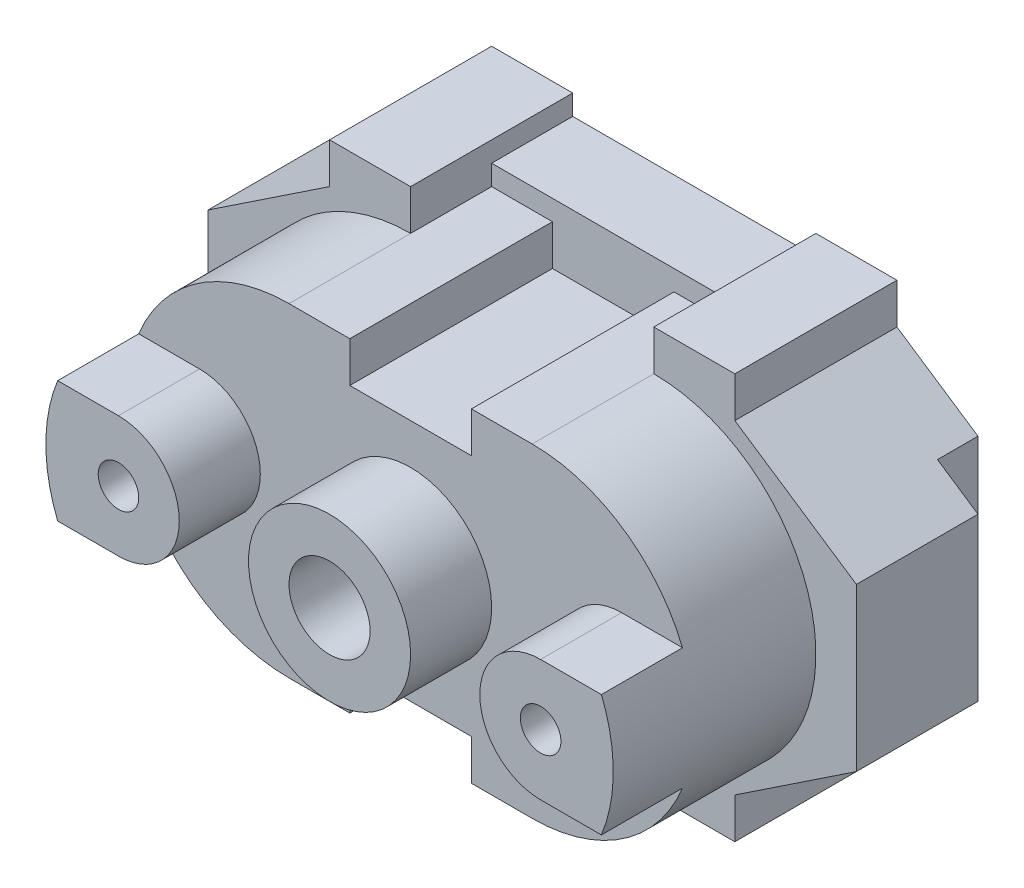
SolidWorks part; units mm, degrees
ref_plane "Front Plane" through (0, 0, 0) normal (0, 0, 1) x (1, 0, 0)
ref_plane "Top Plane" through (0, 0, 0) normal (0, 1, 0) x (1, 0, 0)
ref_plane "Right Plane" through (0, 0, 0) normal (1, 0, 0) x (0, 0, -1)
sketch "Sketch1" plane through (0, 0, 0) normal (0, 0, 1) x (1, 0, 0)
  line L0 (-80, 0) -> (-65, 10)
  line L1 (-65, 10) -> (-65, 15)
  line L2 (-65, 15) -> (-55, 15)
  line L3 (-55, 15) -> (-55, 10)
  line L4 (-55, 10) -> (-25, 10)
  line L5 (-25, 10) -> (-25, 15)
  line L6 (-25, 15) -> (-15, 15)
  line L7 (-15, 15) -> (-15, 10)
  line L8 (-15, 10) -> (0, 0)
  line L9 (0, 0) -> (0, -20)
  line L10 (0, -20) -> (-15, -30)
  line L11 (-15, -30) -> (-15, -35)
  line L12 (-15, -35) -> (-25, -35)
  line L13 (-25, -35) -> (-25, -30)
  line L14 (-25, -30) -> (-55, -30)
  line L15 (-55, -30) -> (-55, -35)
  line L16 (-55, -35) -> (-65, -35)
  line L17 (-65, -35) -> (-65, -30)
  line L18 (-65, -30) -> (-80, -20)
  line L19 (-80, -20) -> (-80, 0)
  dimension "D1" = 10
  dimension "D2" = 10
  dimension "D3" = 5
  dimension "D4" = 5
  dimension "D5" = 5
  dimension "D6" = 5
  dimension "D7" = 20
  dimension "D8" = 20
  dimension "D9" = 5
  dimension "D10" = 10
  dimension "D11" = 5
  dimension "D12" = 30
  dimension "D13" = 15
  dimension "D14" = 10
  dimension "D15" = 5
  dimension "D16" = 5
  dimension "D17" = 10
  dimension "D18" = 15
  dimension "D19" = 10
  dimension "D20" = 15
  dimension "D21" = 10
  dimension "D22" = 15
extrude "Boss-Extrude1" add sketch "Sketch1" along normal blind 20
sketch "Sketch2" plane through (-80, 0, 0) normal (-1, 0, 0) x (0, 0, 1)
  line L1 (0, -23.75) -> (0, 3.75)
  line L2 (0, 3.75) -> (5, 3.75)
  line L3 (5, 3.75) -> (5, -23.75)
  line L4 (5, -23.75) -> (0, -23.75)
  line L5 (20, -20) -> (0, -20) construction
  dimension "D1" = 27.5
  dimension "D2" = 5
  dimension "D3" = 3.75
extrude "Cut-Extrude2" cut sketch "Sketch2" against normal blind 5
sketch "Sketch3" plane through (0, 0, 0) normal (1, 0, 0) x (0, 0, -1)
  line L0 (0, 3.75) -> (0, -23.75)
  line L1 (0, -23.75) -> (-5, -23.75)
  line L2 (-5, -23.75) -> (-5, 3.75)
  line L3 (-5, 3.75) -> (0, 3.75)
  line L4 (-20, 0) -> (0, 0) construction
  dimension "D1" = 5
  dimension "D2" = 27.5
  dimension "D3" = 3.75
extrude "Cut-Extrude3" cut sketch "Sketch3" against normal blind 5
sketch "Sketch4" plane through (0, 0, 20) normal (0, 0, 1) x (1, 0, 0)
  line L0 (-55, -10) -> (-25, -10) construction
  line L1 (-55, 10) -> (-25, 10)
  line L2 (-55, -30) -> (-25, -30)
  arc A0 (-55, 10) -> (-55, -30) centre (-55, -10) ccw
  arc A1 (-25, -30) -> (-25, 10) centre (-25, -10) ccw
  point P2 (-40, -10)
  dimension "D1" = 20
extrude "Boss-Extrude2" add sketch "Sketch4" along normal blind 15
sketch "Sketch5" plane through (0, 0, 0) normal (0, 0, -1) x (-1, 0, 0)
  line L0 (25, -32.5) -> (25, -30)
  line L1 (25, -30) -> (25, -35) construction
  line L2 (25, -30) -> (55, -30)
  line L3 (55, -30) -> (55, -32.5)
  line L4 (55, -35) -> (55, -30) construction
  line L5 (55, -32.5) -> (25, -32.5)
  line L7 (25, 12.5) -> (25, 10)
  line L8 (25, 15) -> (25, 10) construction
  line L9 (25, 10) -> (55, 10)
  line L10 (55, 10) -> (55, 12.5)
  line L11 (55, 10) -> (55, 15) construction
  line L12 (55, 12.5) -> (25, 12.5)
extrude "Boss-Extrude3" add sketch "Sketch5" against normal blind 10
sketch "Sketch6" plane through (0, 0, 35) normal (0, 0, 1) x (1, 0, 0)
  line L0 (-47.5, -30) -> (-47.5, -25)
  line L1 (-55, -30) -> (-25, -30) construction
  line L2 (-47.5, -25) -> (-32.5, -25)
  line L3 (-32.5, -25) -> (-32.5, -30)
  line L4 (-32.5, -30) -> (-47.5, -30)
  line L5 (-47.5, 10) -> (-47.5, 5)
  line L6 (-25, 10) -> (-55, 10) construction
  line L7 (-47.5, 5) -> (-32.5, 5)
  line L8 (-32.5, 5) -> (-32.5, 10)
  line L9 (-32.5, 10) -> (-47.5, 10)
  dimension "D1" = 7.5
  dimension "D2" = 7.5
  dimension "D3" = 5
  dimension "D4" = 7.5
  dimension "D5" = 7.5
  dimension "D6" = 5
extrude "Cut-Extrude4" cut sketch "Sketch6" against normal blind 25
sketch "Sketch7" plane through (0, 0, 35) normal (0, 0, 1) x (1, 0, 0)
  line L0 (-47.5, 5) -> (-32.5, 5) construction
  circle A0 centre (-40, -10) radius 10
  point P2 (-40, 5)
  dimension "D1" = 20
  dimension "D2" = 15
extrude "Boss-Extrude4" add sketch "Sketch7" along normal blind 10
sketch "Sketch8" plane through (0, 0, 45) normal (0, 0, 1) x (1, 0, 0)
  circle A0 centre (-40, -10) radius 5
  dimension "D1" = 10
extrude "Cut-Extrude5" cut sketch "Sketch8" against normal blind 310
sketch "Sketch10" plane through (0, 0, 35) normal (0, 0, 1) x (1, 0, 0)
  line L0 (-73.5405, -17.5) -> (-66.0405, -17.5)
  line L1 (-73.5405, -2.5) -> (-66.0405, -2.5)
  line L2 (-6.4595, -17.5) -> (-13.9595, -17.5)
  line L3 (-13.9595, -2.5) -> (-6.4595, -2.5)
  arc A0 (-55, 10) -> (-55, -30) centre (-55, -10) ccw construction
  arc A1 (-66.0405, -17.5) -> (-66.0405, -2.5) centre (-66.0405, -10) ccw
  arc A2 (-73.5405, -2.5) -> (-73.5405, -17.5) centre (-55, -10) ccw
  arc A3 (-25, -30) -> (-25, 10) centre (-25, -10) ccw construction
  arc A4 (-13.9595, -17.5) -> (-13.9595, -2.5) centre (-13.9595, -10) cw
  arc A5 (-25, -30) -> (-25, 10) centre (-25, -10) ccw construction
  arc A6 (-6.4595, -17.5) -> (-6.4595, -2.5) centre (-25, -10) ccw
  point P21 (-40, -10)
  dimension "D1" = 7.5
  dimension "D2" = 20
  dimension "D3" = 7.5
  dimension "D4" = 20
  dimension "D5" = 7.5
  dimension "D6" = 7.5
extrude "Boss-Extrude5" add sketch "Sketch10" along normal blind 10
sketch "Sketch11" plane through (0, 0, 45) normal (0, 0, 1) x (1, 0, 0)
  circle A0 centre (-66.0405, -10) radius 2.5
  circle A1 centre (-13.9595, -10) radius 2.5
  dimension "D1" = 5
  dimension "D2" = 5
extrude "Cut-Extrude6" cut sketch "Sketch11" against normal blind 300
